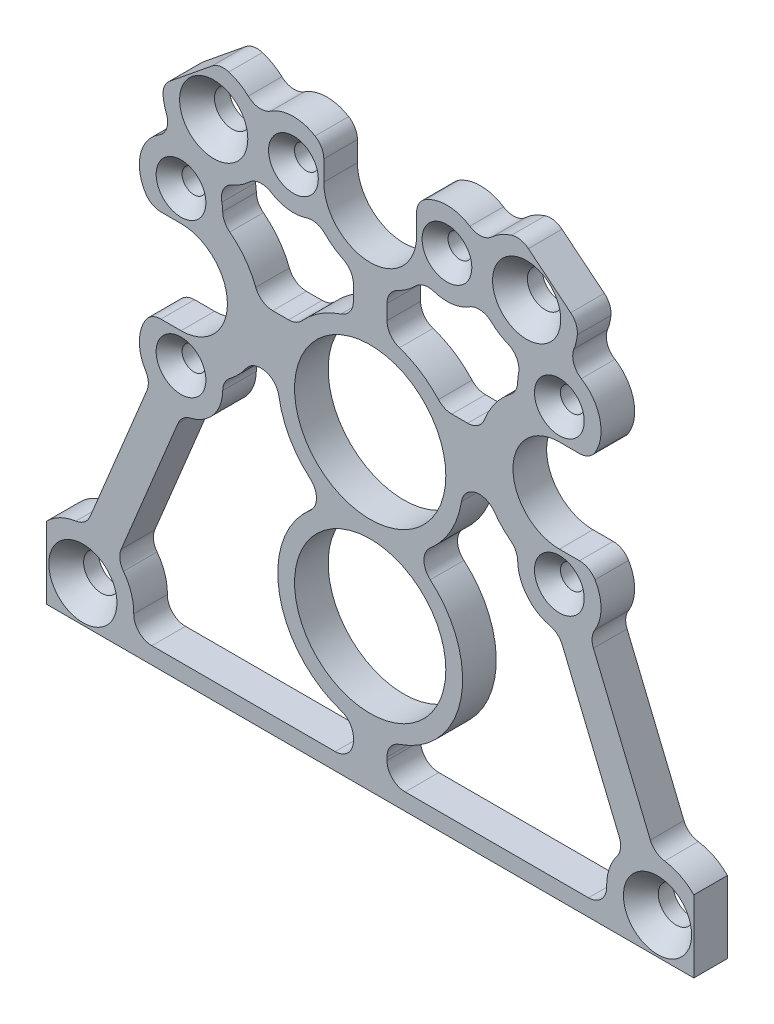
SolidWorks part; units mm, degrees
material "6061-T6 (SS)"
ref_plane "Front Plane" through (0, 0, 0) normal (0, 0, 1) x (1, 0, 0)
ref_plane "Top Plane" through (0, 0, 0) normal (0, 1, 0) x (1, 0, 0)
ref_plane "Right Plane" through (0, 0, 0) normal (1, 0, 0) x (0, 0, -1)
sketch "Sketch1" plane through (0, 0, 0) normal (0, 0, 1) x (1, 0, 0)
  line L0 (-35.7363, 39.2389) -> (0, 68.2625) construction
  line L1 (0, 68.2625) -> (35.7363, 39.2389) construction
  line L2 (-61.1363, -26.9875) -> (61.1363, -26.9875)
  line L3 (61.1363, -26.9875) -> (61.1363, 39.2389)
  line L4 (51.7493, 58.9554) -> (16.013, 87.9791)
  line L5 (-16.013, 87.9791) -> (-51.7493, 58.9554)
  line L6 (-61.1363, 39.2389) -> (-61.1363, -26.9875)
  line L7 (-1122.9756, 17.0139) -> (48877.0244, 17.0139) construction
  circle A0 centre (0, 68.2625) radius 8.763
  circle A1 centre (0, 68.2625) radius 22.225 construction
  circle A2 centre (0, 68.2625) radius 4.7625 construction
  circle A3 centre (-35.7363, 39.2389) radius 4.7625 construction
  circle A4 centre (-35.7363, 39.2389) radius 8.763
  circle A5 centre (-35.7363, 39.2389) radius 22.225 construction
  circle A6 centre (35.7363, 39.2389) radius 4.7625 construction
  circle A7 centre (35.7363, 39.2389) radius 8.763
  circle A8 centre (35.7363, 39.2389) radius 22.225 construction
  circle A9 centre (0, 31.75) radius 31.75 construction
  circle A10 centre (0, 31.75) radius 7.9375 construction
  circle A11 centre (0, 0) radius 23.8125 construction
  circle A12 centre (0, 31.75) radius 14.2875
  circle A13 centre (0, 0) radius 14.2875
  arc A14 (-61.1363, 39.2389) -> (-51.7493, 58.9554) centre (-35.7363, 39.2389) cw
  arc A15 (-16.013, 87.9791) -> (16.013, 87.9791) centre (0, 68.2625) cw
  arc A16 (51.7493, 58.9554) -> (61.1363, 39.2389) centre (35.7363, 39.2389) cw
  dimension "D1" = 44.45
  dimension "D2" = 9.525
  dimension "D3" = 17.526
  dimension "D4" = 63.5
  dimension "D5" = 15.875
  dimension "D6" = 47.625
  dimension "D7" = 28.575
  dimension "D8" = 28.575
  dimension "D9" = 3.175
  dimension "D10" = 3.175
  dimension "D11" = 3.175
  dimension "D14" = 1.5875
  dimension "D12" = 3.175
  dimension "D13" = 17.0139
extrude "Boss-Extrude1" add sketch "Sketch1" along normal blind 6.35
hole_wizard "CSK for 1/4 Flat Head Machine Screw1" positions "Sketch2" profile "Sketch3" countersink size "1/4" standard "ANSI Inch" end condition through all
sketch "Sketch2" plane through (0, 0, 6.35) normal (0, 0, 1) x (1, 0, 0)
  line L0 (-54.2783, -20.1295) -> (0, 0) construction
  line L1 (0, 0) -> (54.2783, -20.1295) construction
  line L4 (-29.5576, 68.1438) -> (0, 0) construction
  line L5 (0, 0) -> (29.5576, 68.1438) construction
  line L8 (-61.1363, -26.9875) -> (61.1363, -26.9875) construction
  line L9 (-61.1363, 39.2389) -> (-61.1363, -26.9875) construction
  line L10 (-16.013, 87.9791) -> (-51.7493, 58.9554) construction
  line L11 (-35.7363, 39.2389) -> (-29.5576, 68.1438) construction
  line L12 (-29.5576, 68.1438) -> (0, 68.2625) construction
  point P0 (29.5576, 68.1438)
  point P2 (-29.5576, 68.1438)
  point P4 (54.2783, -20.1295)
  point P6 (-54.2783, -20.1295)
  dimension "D1" = 6.858
  dimension "D2" = 6.858
  dimension "D3" = 6.858
sketch "Sketch3" plane through (29.5576, 68.1438, 6.35) normal (1, 0, 0) x (0, -1, 0)
  line L0 (0, 0) -> (0, 6.35)
  line L1 (0, 6.35) -> (3.3782, 6.35)
  line L2 (3.3782, 6.35) -> (3.3782, 3.5209)
  line L3 (3.3782, 3.5209) -> (6.4389, 0)
  line L5 (6.4389, 0) -> (0, 0)
  line L6 (-3.3782, 3.5209) -> (-6.4389, 0) construction
  line L11 (0, -6.35) -> (0, 107.95) construction
  dimension "Thru Hole Dia." = 6.7564
  dimension "Thru Hole Depth" = 6.35
  dimension "Near C'Sink Dia." = 12.8778
  dimension "Near C'Sink Angle" = 82
hole_wizard "CSK for M4 Flat Head Machine Screw1" positions "Sketch5" profile "Sketch6" countersink size "M4" standard "ANSI Metric" end condition through all
sketch "Sketch5" plane through (0, 0, 6.35) normal (0, 0, 1) x (1, 0, 0)
  circle A0 centre (-35.7363, 39.2389) radius 14.5
  circle A1 centre (35.7363, 39.2389) radius 14.5
  circle A2 centre (0, 68.2625) radius 14.5
  point P0 (-35.7363, 24.7389)
  point P2 (-35.7363, 53.7389)
  point P4 (35.7363, 24.7389)
  point P6 (35.7363, 53.7389)
  point P8 (-14.5, 68.2625)
  point P10 (14.5, 68.2625)
  dimension "D1" = 29
sketch "Sketch6" plane through (-35.7363, 24.7389, 6.35) normal (1, 0, 0) x (0, -1, 0)
  line L0 (0, 0) -> (0, 6.35)
  line L1 (0, 6.35) -> (2.25, 6.35)
  line L2 (2.25, 6.35) -> (2.25, 2.45)
  line L3 (2.25, 2.45) -> (4.7, 0)
  line L5 (4.7, 0) -> (0, 0)
  line L6 (-2.25, 2.45) -> (-4.7, 0) construction
  line L11 (0, -6.35) -> (0, 107.95) construction
  dimension "Thru Hole Dia." = 4.5
  dimension "Thru Hole Depth" = 6.35
  dimension "Near C'Sink Dia." = 9.4
  dimension "Near C'Sink Angle" = 90
sketch "Sketch4" plane through (0, 0, 6.35) normal (0, 0, 1) x (1, 0, 0)
  line L0 (51.7493, 58.9554) -> (16.013, 87.9791) construction
  line L1 (35.7363, 39.2389) -> (58.6698, 50.1574) construction
  line L2 (61.1363, -26.9875) -> (61.1363, 39.2389) construction
  line L3 (61.1363, -13.3919) -> (61.1363, 39.2389)
  line L4 (51.7493, 58.9554) -> (39.1112, 69.2196)
  line L5 (35.7363, 24.7389) -> (54.2783, -20.1295) construction
  line L6 (35.5543, 16.866) -> (47.8782, -12.9555)
  line L7 (41.4229, 19.2912) -> (53.7468, -10.5303)
  line L8 (35.7363, 48.0019) -> (41.1309, 48.0019)
  line L9 (32.8019, 23.5262) -> (51.3439, -21.3421) construction
  line L10 (38.6706, 25.9515) -> (57.2126, -18.9169) construction
  line L11 (35.7363, 30.4759) -> (41.1309, 30.4759)
  line L12 (-54.2783, -20.1295) -> (-35.7363, 24.7389) construction
  line L13 (-47.8782, -12.9555) -> (-35.5543, 16.866)
  line L14 (-53.7468, -10.5303) -> (-41.4229, 19.2912)
  line L15 (-41.1309, 30.4759) -> (-35.7363, 30.4759)
  line L16 (-51.3439, -21.3421) -> (-32.8019, 23.5262) construction
  line L17 (-57.2126, -18.9169) -> (-38.6706, 25.9515) construction
  line L18 (-16.013, 87.9791) -> (-51.7493, 58.9554) construction
  line L19 (-61.1363, 39.2389) -> (-61.1363, -26.9875) construction
  line L20 (-39.1112, 69.2196) -> (-51.7493, 58.9554)
  line L21 (-61.1363, 39.2389) -> (-61.1363, -13.3919)
  line L22 (-35.7363, 48.0019) -> (-41.1309, 48.0019)
  line L23 (-35.7363, 48.0019) -> (-35.7363, 30.4759)
  line L24 (-8.763, 68.2625) -> (-8.763, 73.6572)
  line L25 (8.763, 68.2625) -> (8.763, 73.6572)
  line L26 (51.7493, 58.9554) -> (39.1112, 69.2196)
  line L27 (-24.5745, 39.2389) -> (-17.4625, 39.2389) construction
  line L28 (17.4625, 39.2389) -> (24.5745, 39.2389) construction
  line L29 (48.4505, 39.2389) -> (57.9613, 39.2389) construction
  line L30 (-57.9613, -23.8125) -> (57.9613, -23.8125)
  line L31 (-57.9613, 39.2389) -> (-57.9613, -23.8125)
  line L32 (-14.0114, 85.5145) -> (-49.7477, 56.4908)
  line L33 (49.7477, 56.4908) -> (14.0114, 85.5145)
  line L34 (57.9613, -23.8125) -> (57.9613, 39.2389)
  line L35 (-45.3978, -23.8125) -> (-3.175, -23.8125)
  line L36 (-16.013, 87.9791) -> (-28.6512, 77.7148)
  line L37 (-39.1112, 69.2196) -> (-51.7493, 58.9554)
  line L38 (28.6512, 77.7148) -> (16.013, 87.9791)
  line L39 (-8.763, 68.2625) -> (8.763, 68.2625)
  line L40 (-48.4505, 39.2389) -> (-57.9613, 39.2389) construction
  line L41 (0, -17.4625) -> (0, -23.8125) construction
  line L42 (0, 49.2125) -> (0, 56.3245) construction
  line L44 (11.7881, 68.2151) -> (21.8944, 68.1745) construction
  line L45 (-11.7881, 68.2151) -> (-21.8944, 68.1745) construction
  line L47 (21.6676, 65.0004) -> (20.4705, 65.0052)
  line L53 (-3.175, -17.1714) -> (-3.175, -23.8125)
  line L54 (3.175, 48.9214) -> (3.175, 56.7544)
  line L55 (-21.6676, 65.0004) -> (-20.4705, 65.0052)
  line L59 (-20.9605, 42.4139) -> (-13.8283, 42.4139)
  line L60 (13.8283, 42.4139) -> (20.9605, 42.4139)
  line L62 (3.175, -17.1714) -> (3.175, -23.8125)
  line L63 (-3.175, 48.9214) -> (-3.175, 56.7544)
  line L67 (11.7754, 65.0402) -> (21.8816, 64.9996) construction
  line L68 (3.175, 49.2125) -> (3.175, 56.3245) construction
  line L69 (-3.175, 49.2125) -> (-3.175, 56.3245) construction
  line L70 (-11.7754, 65.0402) -> (-21.8816, 64.9996) construction
  line L73 (17.4625, 42.4139) -> (24.5745, 42.4139) construction
  line L76 (-24.5745, 42.4139) -> (-17.4625, 42.4139) construction
  line L80 (3.175, -17.4625) -> (3.175, -23.8125) construction
  line L81 (-3.175, -17.4625) -> (-3.175, -23.8125) construction
  line L82 (3.175, -23.8125) -> (45.3978, -23.8125)
  arc A0 (61.1363, 39.2389) -> (51.7493, 58.9554) centre (35.7363, 39.2389) ccw construction
  arc A1 (41.1309, 48.0019) -> (39.8822, 60.4341) centre (35.7363, 53.7389) ccw
  circle A2 centre (0, 31.75) radius 17.4625
  arc A3 (-3.175, 48.9214) -> (-13.8283, 42.4139) centre (0, 31.75) ccw
  circle A4 centre (-35.7363, 53.7389) radius 7.875
  circle A5 centre (0, 68.2625) radius 8.763 construction
  arc A6 (-20.9605, 42.4139) -> (-28.0079, 52.2263) centre (-35.7363, 39.2389) ccw
  arc A7 (-28.0079, 52.2263) -> (-28.0277, 55.3495) centre (-35.7363, 53.7389) ccw
  circle A8 centre (0, 0) radius 17.4625
  arc A9 (-7.2748, 15.875) -> (-3.175, -17.1714) centre (0, 0) ccw
  arc A10 (38.4985, 64.6099) -> (39.1112, 69.2196) centre (29.5576, 68.1438) ccw
  circle A11 centre (-14.5, 68.2625) radius 4.7 construction
  arc A12 (23.427, 30.4704) -> (28.0079, 26.2514) centre (35.7363, 39.2389) ccw
  circle A13 centre (-35.7363, 24.7389) radius 7.875
  arc A14 (-18.8179, 74.8482) -> (-8.763, 73.6572) centre (-14.5, 68.2625) cw
  arc A15 (8.763, 73.6572) -> (18.8179, 74.8482) centre (14.5, 68.2625) cw
  arc A16 (-28.6512, 77.7148) -> (-23.0272, 75.1993) centre (-29.5576, 68.1438) cw
  circle A17 centre (-29.5576, 68.1438) radius 9.6139
  arc A18 (-25.9559, 59.2301) -> (-20.4705, 65.0052) centre (-29.5576, 68.1438) ccw
  arc A19 (20.4705, 65.0052) -> (25.9559, 59.2301) centre (29.5576, 68.1438) ccw
  circle A20 centre (29.5576, 68.1438) radius 6.4389 construction
  circle A21 centre (35.7363, 53.7389) radius 4.7 construction
  arc A22 (23.0272, 75.1993) -> (28.6512, 77.7148) centre (29.5576, 68.1438) cw
  circle A23 centre (-54.2783, -20.1295) radius 9.6139
  arc A24 (-45.3978, -23.8125) -> (-47.8782, -12.9555) centre (-54.2783, -20.1295) ccw
  arc A25 (-41.1309, 30.4759) -> (-41.4229, 19.2912) centre (-35.7363, 24.7389) ccw
  circle A26 centre (54.2783, -20.1295) radius 9.6139
  arc A27 (61.1363, -13.3919) -> (53.7468, -10.5303) centre (54.2783, -20.1295) ccw
  arc A28 (38.4985, 64.6099) -> (39.8822, 60.4341) centre (41.6874, 63.3495) ccw
  arc A29 (-23.0272, 75.1993) -> (-18.8179, 74.8482) centre (-20.698, 77.7158) ccw
  arc A30 (18.8179, 74.8482) -> (23.0272, 75.1993) centre (20.698, 77.7158) ccw
  circle A31 centre (35.7363, 39.2389) radius 8.763 construction
  circle A32 centre (14.5, 68.2625) radius 7.875
  arc A33 (10.0259, 61.7819) -> (21.6676, 65.0004) centre (14.5, 68.2625) ccw
  arc A34 (61.1363, 39.2389) -> (51.7493, 58.9554) centre (35.7363, 39.2389) ccw
  arc A35 (41.4229, 19.2912) -> (41.1309, 30.4759) centre (35.7363, 24.7389) ccw
  arc A36 (47.8782, -12.9555) -> (45.3978, -23.8125) centre (54.2783, -20.1295) ccw
  arc A37 (-41.1309, 48.0019) -> (-39.8822, 60.4341) centre (-35.7363, 53.7389) cw
  circle A38 centre (35.7363, 24.7389) radius 7.875
  arc A39 (-49.7477, 56.4908) -> (-57.9613, 39.2389) centre (-35.7363, 39.2389) ccw
  arc A40 (14.0114, 85.5145) -> (-14.0114, 85.5145) centre (0, 68.2625) ccw
  arc A41 (57.9613, 39.2389) -> (49.7477, 56.4908) centre (35.7363, 39.2389) ccw
  arc A42 (-38.4985, 64.6099) -> (-39.1112, 69.2196) centre (-29.5576, 68.1438) cw
  arc A43 (16.013, 87.9791) -> (-16.013, 87.9791) centre (0, 68.2625) ccw construction
  arc A44 (35.7363, 30.4759) -> (35.7363, 48.0019) centre (35.7363, 39.2389) ccw
  arc A45 (-53.7468, -10.5303) -> (-61.1363, -13.3919) centre (-54.2783, -20.1295) ccw
  arc A46 (-10.0259, 61.7819) -> (-3.175, 56.7544) centre (0, 68.2625) ccw
  arc A47 (3.175, 56.7544) -> (10.0259, 61.7819) centre (0, 68.2625) ccw
  arc A48 (13.8283, 42.4139) -> (3.175, 48.9214) centre (0, 31.75) ccw
  arc A49 (-35.5543, 16.866) -> (-28.0079, 26.2514) centre (-35.7363, 24.7389) ccw
  arc A50 (7.2748, 15.875) -> (17.2474, 29.0175) centre (0, 31.75) ccw
  arc A51 (-17.2474, 29.0175) -> (-7.2748, 15.875) centre (0, 31.75) ccw
  circle A52 centre (-35.7363, 39.2389) radius 8.763 construction
  arc A53 (3.175, -17.1714) -> (7.2748, 15.875) centre (0, 0) ccw
  arc A54 (28.0079, 26.2514) -> (35.5543, 16.866) centre (35.7363, 24.7389) ccw
  arc A55 (-28.0079, 26.2514) -> (-23.427, 30.4704) centre (-35.7363, 39.2389) ccw
  arc A56 (-51.7493, 58.9554) -> (-61.1363, 39.2389) centre (-35.7363, 39.2389) ccw construction
  arc A57 (28.0079, 52.2263) -> (20.9605, 42.4139) centre (35.7363, 39.2389) ccw
  arc A58 (16.013, 87.9791) -> (-16.013, 87.9791) centre (0, 68.2625) ccw
  arc A59 (-21.6676, 65.0004) -> (-10.0259, 61.7819) centre (-14.5, 68.2625) ccw
  arc A60 (-39.8822, 60.4341) -> (-38.4985, 64.6099) centre (-41.6874, 63.3495) ccw
  arc A61 (-25.9559, 59.2301) -> (-28.0277, 55.3495) centre (-24.6712, 56.0508) ccw
  arc A62 (-17.2474, 29.0175) -> (-23.427, 30.4704) centre (-20.6342, 28.481) ccw
  arc A63 (28.0277, 55.3495) -> (25.9559, 59.2301) centre (24.6712, 56.0508) ccw
  arc A64 (-51.7493, 58.9554) -> (-61.1363, 39.2389) centre (-35.7363, 39.2389) ccw
  arc A65 (23.427, 30.4704) -> (17.2474, 29.0175) centre (20.6342, 28.481) ccw
  arc A67 (28.0277, 55.3495) -> (28.0079, 52.2263) centre (35.7363, 53.7389) ccw
  dimension "D19" = 6.858
  dimension "D7" = 3.175
  dimension "D17" = 3.175
  dimension "D4" = 6.35
  dimension "D5" = 3.175
  dimension "D1" = 3.175
  dimension "D3" = 3.175
  dimension "D6" = 3.175
  dimension "D8" = 3.175
  dimension "D9" = 3.175
  dimension "D10" = 3.175
  dimension "D11" = 3.175
  dimension "D12" = 3.175
  dimension "D13" = 3.175
  dimension "D14" = 3.175
  dimension "D16" = 3.175
  dimension "D18" = 3.175
  dimension "D20" = 3.175
  dimension "D21" = 3.175
  dimension "D22" = 3.175
  dimension "D23" = 3.175
extrude "Cut-Extrude1" cut sketch "Sketch4" against normal through all
fillet "Fillet1" radius 3.429 42 edges at (13.8283, 42.4139, 3.175) (3.175, -23.8125, 3.175) (3.175, -17.1714, 3.175) (7.2748, 15.875, 3.175) (3.175, 56.7544, 3.175) (3.175, 48.9214, 3.175) (-3.175, 48.9214, 3.175) (-13.8283, 42.4139, 3.175) (-20.9605, 42.4139, 3.175) (-3.175, 56.7544, 3.175) (-7.2748, 15.875, 3.175) (-3.175, -17.1714, 3.175) (-3.175, -23.8125, 3.175) (-45.3978, -23.8125, 3.175) (10.0259, 61.7819, 3.175) (-10.0259, 61.7819, 3.175) (28.0079, 26.2514, 3.175) (20.9605, 42.4139, 3.175) (28.0079, 52.2263, 3.175) (-28.0079, 52.2263, 3.175) (39.1112, 69.2196, 3.175) (41.1309, 48.0019, 3.175) (41.1309, 30.4759, 3.175) (53.7468, -10.5303, 3.175) (41.4229, 19.2912, 3.175) (35.5543, 16.866, 3.175) (47.8782, -12.9555, 3.175) (45.3978, -23.8125, 3.175) (-35.5543, 16.866, 3.175) (-28.0079, 26.2514, 3.175) (-47.8782, -12.9555, 3.175) (-53.7468, -10.5303, 3.175) (-41.4229, 19.2912, 3.175) (-41.1309, 30.4759, 3.175) (-41.1309, 48.0019, 3.175) (-39.1112, 69.2196, 3.175) (28.6512, 77.7148, 3.175) (-28.6512, 77.7148, 3.175) (-8.763, 73.6572, 3.175) (8.763, 73.6572, 3.175) (20.9842, 63.7937, 3.175) (-20.9842, 63.7937, 3.175)
